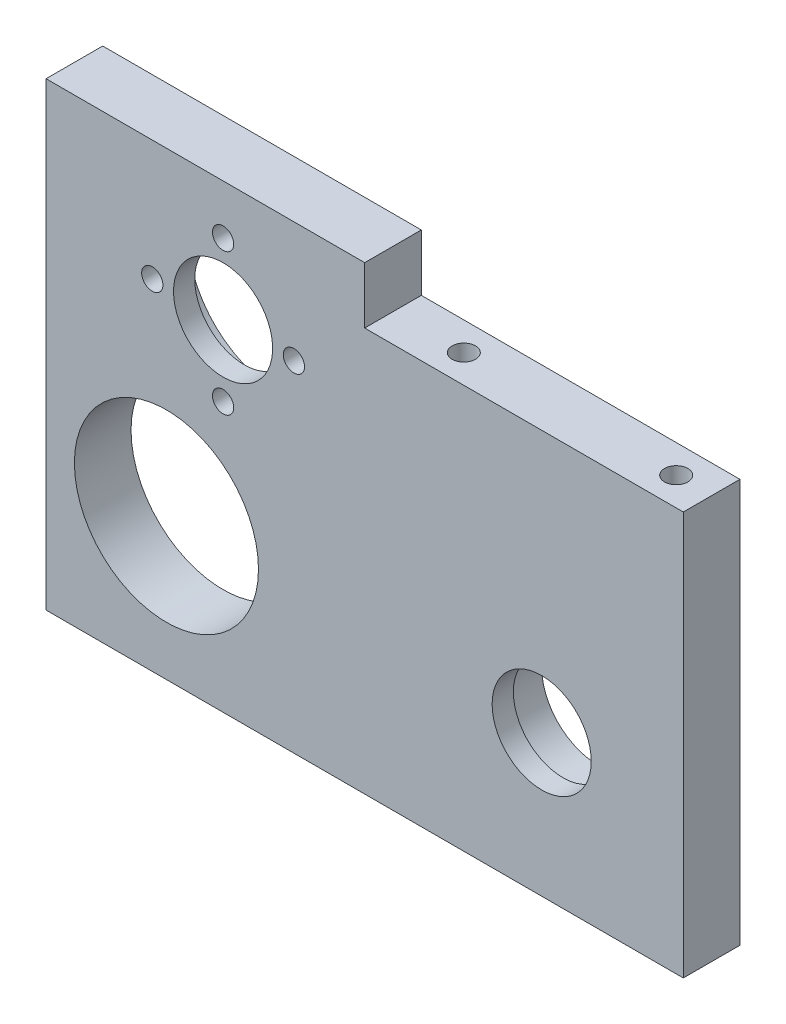
SolidWorks part; units mm, degrees
ref_plane "Front" through (0, 0, 0) normal (0, 0, 1) x (1, 0, 0)
ref_plane "Top" through (0, 0, 0) normal (0, 1, 0) x (1, 0, 0)
ref_plane "Right" through (0, 0, 0) normal (1, 0, 0) x (0, 0, -1)
sketch "Esquisse1" plane through (0, 0, 0) normal (0, 0, 1) x (1, 0, 0)
  line L1 (0, 0) -> (90, 0)
  line L2 (0, 0) -> (0, 65)
  line L3 (0, 65) -> (90, 65)
  line L4 (90, 0) -> (90, 65)
  circle A0 centre (70, 20) radius 7
  circle A1 centre (17, 20) radius 13
  circle A2 centre (25, 48) radius 13
  dimension "D3" = 14
  dimension "D4" = 20
  dimension "D6" = 53
  dimension "D8" = 26
  dimension "D9" = 26
  dimension "D1" = 90
  dimension "D2" = 65
  dimension "D5" = 70
  dimension "D7" = 20
  dimension "D10" = 53
  dimension "D11" = 48
extrude "Boss.-Extru.1" add sketch "Esquisse1" along normal blind 8
sketch "Esquisse2" plane through (0, 0, 0) normal (0, 0, -1) x (-1, 0, 0)
  circle A0 centre (-25, 48) radius 13
  circle A1 centre (-17, 20) radius 13 construction
extrude "Boss.-Extru.2" add sketch "Esquisse2" along normal blind 3 from surface at -8 starting at face at (45, 32.5, 8)
sketch "Esquisse3" plane through (0, 0, 5) normal (0, 0, -1) x (-1, 0, 0)
  line L0 (-15, 48) -> (-25, 48) construction
  circle A0 centre (-25, 48) radius 7
  circle A1 centre (-15, 48) radius 1.5
  circle A2 centre (-25, 38) radius 1.5
  circle A3 centre (-35, 48) radius 1.5
  circle A4 centre (-25, 58) radius 1.5
  point P13 (-25, 48)
  dimension "D1" = 14
  dimension "D2" = 3
  dimension "D3" = 10
  dimension "D4" = 4
extrude "Enlèv. mat.-Extru.1" cut sketch "Esquisse3" against normal through all
sketch "Esquisse4" plane through (0, 0, 8) normal (0, 0, 1) x (1, 0, 0)
  circle A0 centre (70, 20) radius 8
  dimension "D1" = 16
extrude "Enlèv. mat.-Extru.2" cut sketch "Esquisse4" along normal blind 5 from surface at -8 starting at face at (30, 20, 0)
sketch "Esquisse5" plane through (0, 0, 0) normal (0, 0, -1) x (-1, 0, 0)
  line L1 (-90, 65) -> (-45, 65)
  line L2 (-90, 65) -> (-90, 57)
  line L3 (-90, 57) -> (-45, 57)
  line L4 (-45, 65) -> (-45, 57)
  dimension "D1" = 8
  dimension "D2" = 45
extrude "Enlèv. mat.-Extru.3" cut sketch "Esquisse5" against normal through all
sketch "Esquisse6" plane through (0, 0, 0) normal (-1, 0, 0) x (0, 0, 1)
  line L0 (4, 0) -> (4, 45) construction
  line L1 (8, 0) -> (0, 0) construction
  circle A0 centre (4, 45) radius 1.65
  circle A1 centre (4, 7) radius 1.65
  dimension "D1" = 3.3
  dimension "D2" = 38
  dimension "D3" = 7
extrude "Enlèv. mat.-Extru.4" cut sketch "Esquisse6" against normal blind 10
sketch "Esquisse7" plane through (0, 57, 0) normal (0, 1, 0) x (1, 0, 0)
  line L0 (45, -4) -> (85, -4) construction
  line L1 (45, -8) -> (45, 0) construction
  circle A0 centre (85, -4) radius 1.65
  circle A1 centre (55, -4) radius 1.65
  dimension "D1" = 30
  dimension "D2" = 3.3
  dimension "D3" = 10
extrude "Enlèv. mat.-Extru.5" cut sketch "Esquisse7" against normal blind 10
